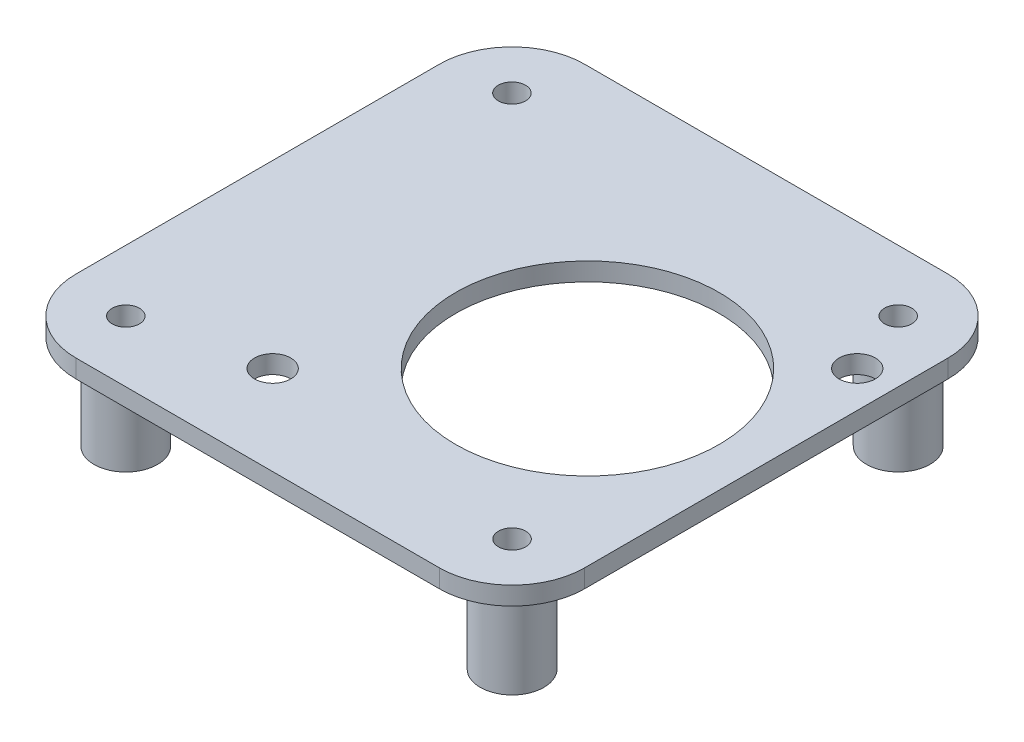
SolidWorks part; units mm, degrees
ref_plane "Front Plane" through (0, 0, 0) normal (0, 0, 1) x (1, 0, 0)
ref_plane "Top Plane" through (0, 0, 0) normal (0, 1, 0) x (1, 0, 0)
ref_plane "Right Plane" through (0, 0, 0) normal (1, 0, 0) x (0, 0, -1)
sketch "Sketch1" plane through (0, 0, 0) normal (0, 1, 0) x (1, 0, 0)
  line L0 (0, 35.56) -> (71.12, 35.56) construction
  line L1 (0, 0) -> (71.12, 0)
  line L2 (0, 0) -> (0, 71.12)
  line L3 (0, 71.12) -> (71.12, 71.12)
  line L4 (71.12, 0) -> (71.12, 71.12)
  line L5 (35.56, 71.12) -> (35.56, 0) construction
  circle A0 centre (8.5598, 62.5475) radius 1.905
  circle A1 centre (62.5475, 62.5602) radius 1.905
  circle A2 centre (62.5602, 8.5725) radius 1.905
  circle A3 centre (8.5725, 8.5598) radius 1.905
  point P7 (35.56, 35.56)
  point P21 (35.56, 35.56)
  dimension "D3" = 3.81
  dimension "D5" = 26.9875
  dimension "D1" = 71.12
  dimension "D2" = 71.12
  dimension "D4" = 27.0002
  dimension "D6" = 4
extrude "Boss-Extrude1" add sketch "Sketch1" along normal blind 2.54
sketch "Sketch2" plane through (0, 2.54, 0) normal (0, 1, 0) x (1, 0, 0)
  line L0 (25.1798, 12.4798) -> (66.04, 53.34) construction
  line L2 (0, 0) -> (71.12, 0) construction
  line L3 (71.12, 0) -> (71.12, 71.12) construction
  line L4 (71.12, 71.12) -> (0, 71.12) construction
  circle A0 centre (25.1798, 12.4798) radius 2.54
  circle A1 centre (66.04, 53.34) radius 2.54
  circle A2 centre (47.1815, 34.4815) radius 18.415
  point P10 (47.1815, 34.4815)
  dimension "D1" = 57.785
  dimension "D3" = 5.08
  dimension "D4" = 5.08
  dimension "D5" = 5.08
  dimension "D8" = 36.83
  dimension "D2" = 45
  dimension "D6" = 17.78
  dimension "D7" = 26.67
extrude "Cut-Extrude1" cut sketch "Sketch2" against normal through all
sketch "Sketch3" plane through (0, 0, 0) normal (0, -1, 0) x (1, 0, 0)
  circle A0 centre (62.5602, -8.5725) radius 1.905
  circle A1 centre (62.5602, -8.5725) radius 1.905 construction
  circle A2 centre (62.5475, -62.5602) radius 1.905
  circle A3 centre (62.5475, -62.5602) radius 1.905 construction
  circle A4 centre (8.5725, -8.5598) radius 1.905
  circle A5 centre (8.5598, -62.5475) radius 1.905
  circle A6 centre (8.5725, -8.5598) radius 1.905 construction
  circle A7 centre (8.5598, -62.5475) radius 1.905 construction
  circle A8 centre (62.5602, -8.5725) radius 4.445
  circle A9 centre (62.5475, -62.5602) radius 4.445
  circle A10 centre (8.5598, -62.5475) radius 4.445
  circle A11 centre (8.5725, -8.5598) radius 4.445
  dimension "D1" = 2.54
extrude "Boss-Extrude2" add sketch "Sketch3" along direction (0, -1, 0) on the side of the normal offset from surface (13.208 mm away) 15.748
fillet "Fillet1" radius 10.16 4 edges at (0, 1.27, 0) (0, 1.27, -71.12) (71.12, 1.27, -71.12) (71.12, 1.27, 0)
